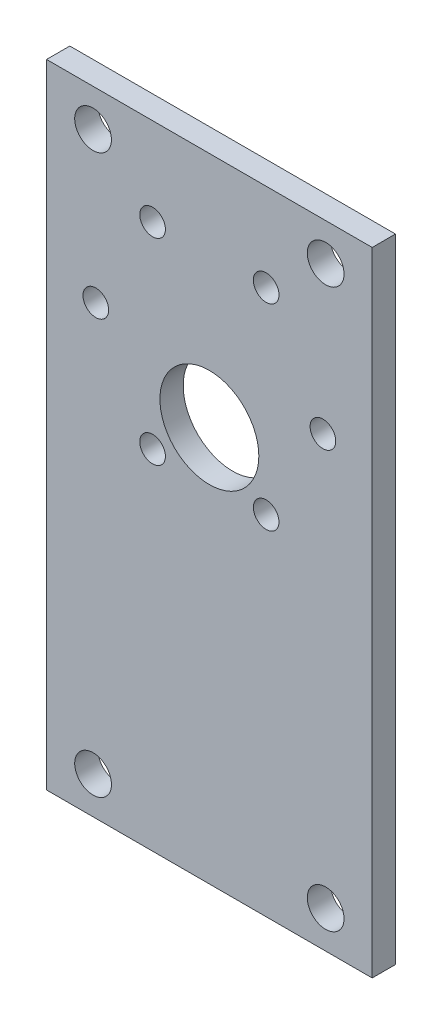
SolidWorks part; units mm, degrees
ref_plane "Спереди" through (0, 0, 0) normal (0, 0, 1) x (1, 0, 0)
ref_plane "Сверху" through (0, 0, 0) normal (0, 1, 0) x (1, 0, 0)
ref_plane "Справа" through (0, 0, 0) normal (1, 0, 0) x (0, 0, -1)
sketch "Эскиз1" plane through (0, 0, 0) normal (0, 0, 1) x (1, 0, 0)
  line L1 (-82.2462, 78.4843) -> (-126.6962, 78.4843)
  line L2 (-82.2462, 78.4843) -> (-82.2462, 27.6843)
  line L4 (-126.6962, 78.4843) -> (-126.6962, 27.6843)
  line L5 (-119.9712, 53.0843) -> (-112.2212, 39.6609) construction
  line L6 (-112.2212, 39.6609) -> (-96.7212, 39.6609) construction
  line L7 (-96.7212, 39.6609) -> (-88.9712, 53.0843) construction
  line L8 (-88.9712, 53.0843) -> (-96.7212, 66.5077) construction
  line L9 (-96.7212, 66.5077) -> (-112.2212, 66.5077) construction
  line L10 (-112.2212, 66.5077) -> (-119.9712, 53.0843) construction
  line L12 (-82.2462, 27.6843) -> (-82.2462, -7.8757)
  line L13 (-82.2462, -7.8757) -> (-126.6962, -7.8757)
  line L14 (-126.6962, 27.6843) -> (-126.6962, -7.8757)
  circle A0 centre (-104.4712, 53.0843) radius 13.4234 construction
  circle A1 centre (-112.2212, 66.5077) radius 1.75
  circle A2 centre (-119.9712, 53.0843) radius 1.75
  circle A3 centre (-112.2212, 39.6609) radius 1.75
  circle A4 centre (-96.7212, 39.6609) radius 1.75
  circle A5 centre (-88.9712, 53.0843) radius 1.75
  circle A6 centre (-96.7212, 66.5077) radius 1.75
  circle A7 centre (-104.4712, 46.0843) radius 6.75
  circle A8 centre (-88.5962, 73.4043) radius 2.5083
  circle A9 centre (-120.3462, 73.4043) radius 2.5083
  circle A10 centre (-88.5962, -2.7957) radius 2.5083
  circle A11 centre (-120.3462, -2.7957) radius 2.5083
  dimension "D6" = 3.5
  dimension "D8" = 13.5
  dimension "D9" = 5.0165
  dimension "D17" = 5.0165
  dimension "D1" = 50.8
  dimension "D2" = 44.45
  dimension "D3" = 25.4
  dimension "D4" = 22.225
  dimension "D5" = 31
  dimension "D7" = 7
  dimension "D10" = 31.75
  dimension "D11" = 6.35
  dimension "D12" = 35.56
  dimension "D13" = 6.35
  dimension "D14" = 31.75
  dimension "D15" = 5.08
  dimension "D16" = 5.08
extrude "Бобышка-Вытянуть1" add sketch "Эскиз1" along normal blind 3.175
